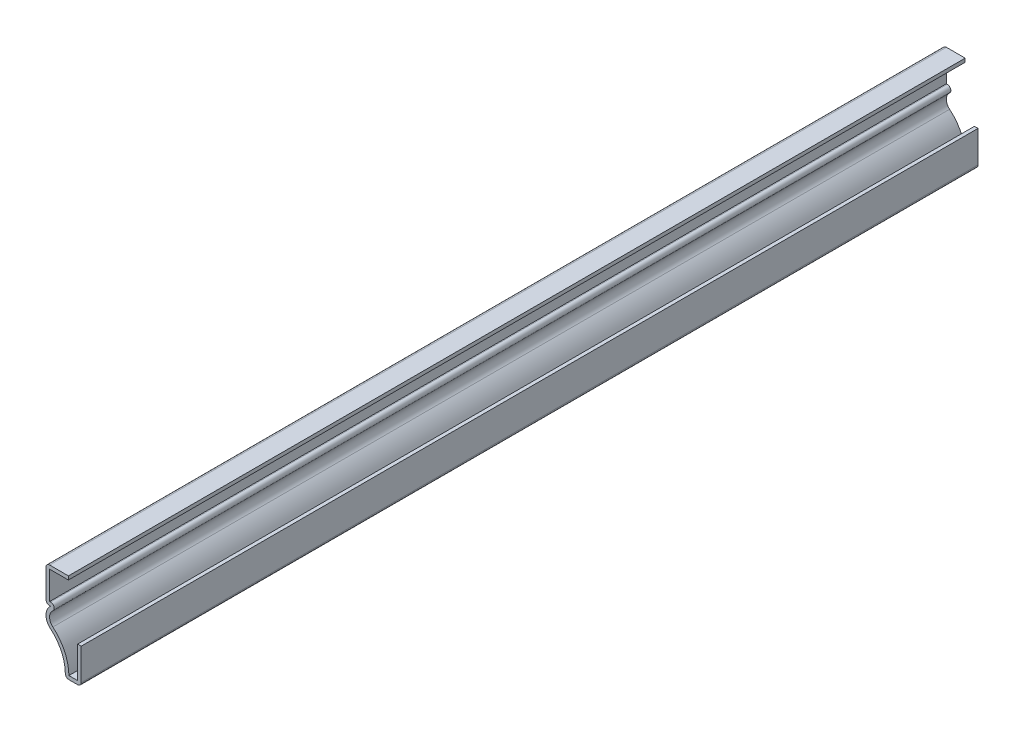
SolidWorks part; units mm, degrees
ref_plane "Front Plane" through (0, 0, 0) normal (0, 0, 1) x (1, 0, 0)
ref_plane "Top Plane" through (0, 0, 0) normal (0, 1, 0) x (1, 0, 0)
ref_plane "Right Plane" through (0, 0, 0) normal (1, 0, 0) x (0, 0, -1)
sketch "Sketch1" plane through (0, 0, 0) normal (0, 0, 1) x (1, 0, 0)
  line L0 (0, 8.7312) -> (0, 0)
  line L1 (0, 0) -> (-3.9688, 0)
  line L2 (-7.6041, 13.4937) -> (-8.7312, 13.4937)
  line L3 (-8.7312, 13.4937) -> (-8.7312, 22.225)
  line L4 (-8.7312, 22.225) -> (-3.175, 22.225)
  line L5 (-7.6041, 14.3827) -> (-7.8422, 14.3827)
  line L6 (-7.8422, 14.3827) -> (-7.8422, 21.336)
  line L7 (-7.8422, 21.336) -> (-3.175, 21.336)
  line L8 (-0.889, 8.7312) -> (-0.889, 0.889)
  line L9 (-0.889, 0.889) -> (-3.0528, 0.889)
  line L10 (-7.6041, 14.3827) -> (-7.8422, 14.3827) construction
  line L11 (-3.175, 22.225) -> (-3.175, 21.336)
  line L12 (0, 8.7312) -> (-0.889, 8.7312)
  arc A0 (-3.9688, 0) -> (-7.6041, 8.6412) centre (-14.2598, 0.7558) ccw
  arc A1 (-7.6041, 8.6412) -> (-7.6041, 13.4937) centre (-5.5562, 11.0675) cw
  arc A2 (-3.0528, 0.889) -> (-7.0307, 9.3206) centre (-14.2598, 0.7558) ccw
  arc A3 (-7.0307, 9.3206) -> (-7.0307, 12.8144) centre (-5.5562, 11.0675) cw
  arc A4 (-7.0307, 9.3206) -> (-7.0307, 12.8144) centre (-5.5562, 11.0675) cw construction
  arc A5 (-7.0307, 12.8144) -> (-7.6041, 14.3827) centre (-7.6041, 13.4938) ccw
  point P8 (-8.7312, 11.0675)
  point P14 (0, 0)
  point P24 (0, 0)
  point P26 (0, 0)
  point P28 (0, 0)
  dimension "D5" = 10.3187
  dimension "D8" = 3.175
  dimension "D11" = 0.889
  dimension "D1" = 22.225
  dimension "D2" = 5.5562
  dimension "D3" = 8.7312
  dimension "D4" = 3.9688
  dimension "D6" = 8.7312
  dimension "D7" = 8.7312
  dimension "D9" = 0.889
  dimension "D10" = 0.889
extrude "Boss-Extrude1" add sketch "Sketch1" against normal blind 222.25
fillet "Fillet1" radius 0.889 4 edges at (-3.9688, 0, -111.125) (-8.7312, 13.4937, -111.125) (-8.7312, 22.225, -111.125) (0, 0, -111.125)
